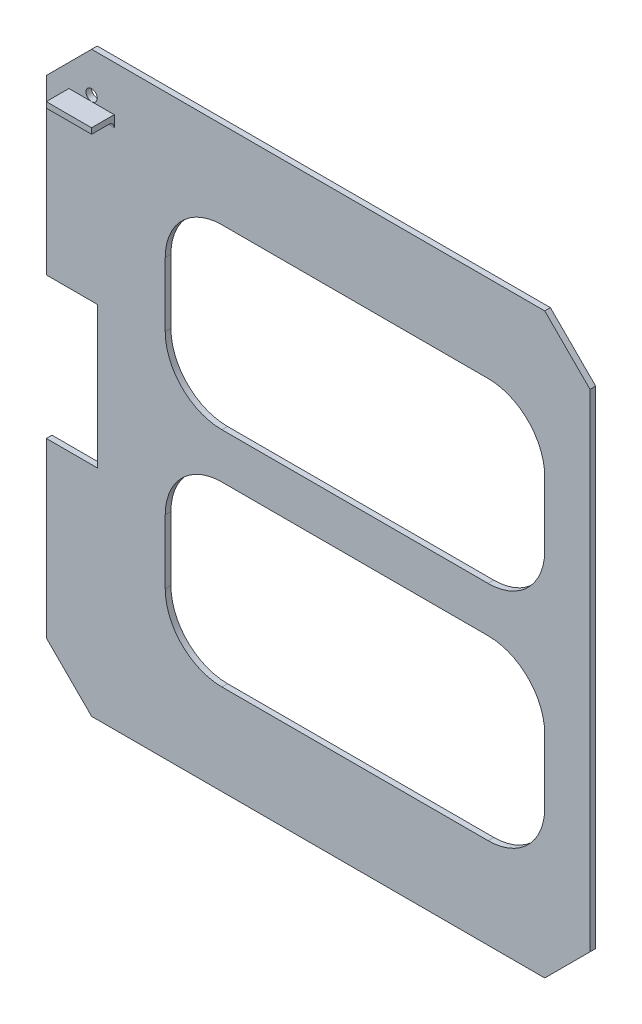
SolidWorks part; units mm, degrees
ref_plane "Front Plane" through (0, 0, 0) normal (0, 0, 1) x (1, 0, 0)
ref_plane "Top Plane" through (0, 0, 0) normal (0, 1, 0) x (1, 0, 0)
ref_plane "Right Plane" through (0, 0, 0) normal (1, 0, 0) x (0, 0, -1)
sketch "Sketch1" plane through (0, 0, 0) normal (0, 0, 1) x (1, 0, 0)
  line L0 (0, 298.45) -> (25.4, 323.85)
  line L1 (25.4, 0) -> (279.4, 0)
  line L2 (0, 25.4) -> (0, 298.45)
  line L3 (25.4, 323.85) -> (279.4, 323.85)
  line L4 (304.8, 25.4) -> (304.8, 298.45)
  line L5 (279.4, 323.85) -> (304.8, 298.45)
  line L6 (25.4, 0) -> (0, 25.4)
  line L7 (279.4, 0) -> (304.8, 25.4)
  point P0 (0, 0)
  point P1 (304.8, 323.85)
  point P2 (0, 323.85)
  point P3 (304.8, 0)
  dimension "D1" = 323.85
  dimension "D2" = 304.8
extrude "Boss-Extrude2" add sketch "Sketch1" along normal blind 3.175
sketch "Sketch4" plane through (0, 0, 3.175) normal (0, 0, 1) x (1, 0, 0)
  line L0 (0, 298.45) -> (0, 25.4) construction
  line L1 (0, 201.6125) -> (28.575, 201.6125)
  line L2 (0, 201.6125) -> (0, 122.2375)
  line L3 (0, 122.2375) -> (28.575, 122.2375)
  line L4 (28.575, 201.6125) -> (28.575, 122.2375)
  line L5 (-28.5301, 161.925) -> (429.1456, 161.925) construction
  line L6 (279.4, 323.85) -> (25.4, 323.85) construction
  dimension "D1" = 79.375
  dimension "D2" = 28.575
  dimension "D3" = 161.925
  dimension "D4" = 39.6875
extrude "Cut-Extrude2" cut sketch "Sketch4" against normal blind 3.175
sketch "Sketch5" plane through (0, 0, 3.175) normal (0, 0, 1) x (1, 0, 0)
  line L0 (28.575, 122.2375) -> (28.575, 201.6125) construction
  line L1 (98.425, 275.1498) -> (247.65, 275.1498)
  line L2 (66.675, 243.3998) -> (66.675, 207.4249)
  line L3 (98.425, 175.6749) -> (247.65, 175.6749)
  line L4 (279.4, 243.3998) -> (279.4, 207.4249)
  line L5 (98.425, 150.2749) -> (247.65, 150.2749)
  line L6 (66.675, 118.5249) -> (66.675, 82.55)
  line L7 (98.425, 50.8) -> (247.65, 50.8)
  line L8 (279.4, 118.5249) -> (279.4, 82.55)
  line L9 (304.8, 25.4) -> (304.8, 298.45) construction
  arc A0 (98.425, 50.8) -> (66.675, 82.55) centre (98.425, 82.55) cw
  arc A1 (247.65, 50.8) -> (279.4, 82.55) centre (247.65, 82.55) ccw
  arc A2 (279.4, 118.5249) -> (247.65, 150.2749) centre (247.65, 118.5249) ccw
  arc A3 (66.675, 118.5249) -> (98.425, 150.2749) centre (98.425, 118.5249) cw
  arc A4 (98.425, 175.6749) -> (66.675, 207.4249) centre (98.425, 207.4249) cw
  arc A5 (279.4, 207.4249) -> (247.65, 175.6749) centre (247.65, 207.4249) cw
  arc A6 (279.4, 243.3998) -> (247.65, 275.1498) centre (247.65, 243.3998) ccw
  arc A7 (66.675, 243.3998) -> (98.425, 275.1498) centre (98.425, 243.3998) cw
  dimension "D8" = 31.75
  dimension "D1" = 38.1
  dimension "D2" = 25.4
  dimension "D3" = 25.4
  dimension "D4" = 25.4
  dimension "D5" = 38.1
  dimension "D6" = 23.3002
  dimension "D7" = 25.4
extrude "Cut-Extrude3" cut sketch "Sketch5" against normal blind 3.175
sketch "Sketch6" plane through (0, 0, 3.175) normal (0, 0, 1) x (1, 0, 0)
  line L0 (0, 298.45) -> (304.8, 298.45) construction
  line L1 (0, 25.4) -> (304.8, 25.4) construction
sketch "Sketch9" plane through (0, 0, 3.175) normal (0, 0, 1) x (1, 0, 0)
  line L0 (279.4, 323.85) -> (25.4, 323.85) construction
  circle A0 centre (25.4, 301.625) radius 3.175
  point P0 (25.4, 301.625)
  dimension "D3" = 6.35
  dimension "D1" = 22.225
  dimension "D2" = 25.4
extrude "Cut-Extrude4" cut sketch "Sketch9" against normal blind 3.175
sketch "Sketch11" plane through (0, 0, 3.175) normal (0, 0, 1) x (1, 0, 0)
  line L0 (0, 298.45) -> (304.8, 298.45) construction
  line L1 (12.7, 298.45) -> (38.1, 298.45)
  line L2 (12.7, 298.45) -> (12.7, 295.275)
  line L3 (12.7, 295.275) -> (38.1, 295.275)
  line L4 (38.1, 298.45) -> (38.1, 295.275)
  line L5 (0, 298.45) -> (0, 201.6125) construction
  dimension "D1" = 3.175
  dimension "D2" = 25.4
  dimension "D3" = 12.7
extrude "Boss-Extrude3" add sketch "Sketch11" along normal blind 12.7
fillet "Fillet2" radius 3.175 1 edges at (25.4, 295.275, 3.175)
